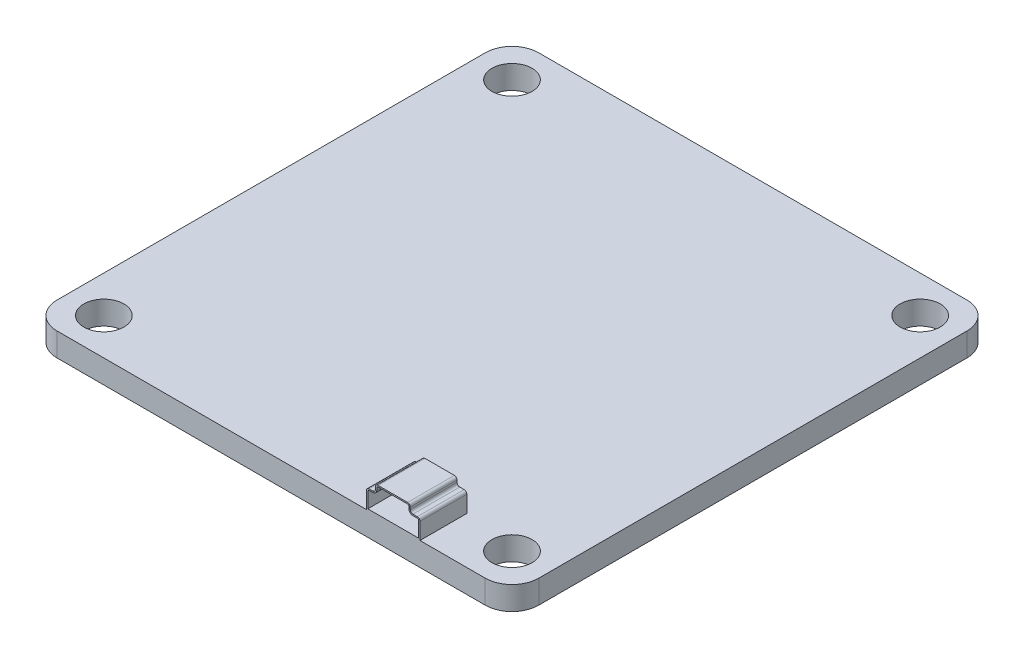
SolidWorks part; units mm, degrees
ref_plane "Front Plane" through (0, 0, 0) normal (0, 0, 1) x (1, 0, 0)
ref_plane "Top Plane" through (0, 0, 0) normal (0, 1, 0) x (1, 0, 0)
ref_plane "Right Plane" through (0, 0, 0) normal (1, 0, 0) x (0, 0, -1)
sketch "Sketch2" plane through (0, 0, 0) normal (0, 1, 0) x (1, 0, 0)
  line L1 (-16, 18) -> (16, 18)
  line L2 (-18, 16) -> (-18, -16)
  line L3 (-16, -18) -> (16, -18)
  line L4 (18, 16) -> (18, -16)
  line L5 (-18, 18) -> (18, -18) construction
  line L6 (-18, -18) -> (18, 18) construction
  line L7 (-15.25, 15.25) -> (15.25, 15.25) construction
  line L8 (-15.25, 15.25) -> (-15.25, -15.25) construction
  line L9 (-15.25, -15.25) -> (15.25, -15.25) construction
  line L10 (15.25, 15.25) -> (15.25, -15.25) construction
  line L11 (-15.25, 15.25) -> (15.25, -15.25) construction
  line L12 (-15.25, -15.25) -> (15.25, 15.25) construction
  circle A0 centre (-15.25, 15.25) radius 1.5
  circle A1 centre (15.25, 15.25) radius 1.5
  circle A2 centre (15.25, -15.25) radius 1.5
  circle A3 centre (-15.25, -15.25) radius 1.5
  arc A4 (16, -18) -> (18, -16) centre (16, -16) ccw
  arc A5 (-18, -16) -> (-16, -18) centre (-16, -16) ccw
  arc A6 (-16, 18) -> (-18, 16) centre (-16, 16) ccw
  arc A7 (16, 18) -> (18, 16) centre (16, 16) cw
  point P0 (0, 0)
  point P6 (0, 0)
  dimension "D5" = 3
  dimension "D6" = 2
  dimension "D1" = 36
  dimension "D2" = 36
  dimension "D3" = 30.5
  dimension "D4" = 30.5
extrude "Boss-Extrude1" add sketch "Sketch2" along normal blind 1.75
sketch "Sketch3" plane through (0, 0, 18) normal (0, 0, 1) x (1, 0, 0)
  line L0 (-16, 1.75) -> (16, 1.75) construction
  line L1 (7.1245, 1.75) -> (11.1245, 1.75)
  line L2 (7.1245, 1.75) -> (7.1245, 2.9923)
  line L3 (7.9938, 3.75) -> (10.1954, 3.75)
  line L4 (11.1245, 1.75) -> (11.1245, 2.9923)
  line L5 (7.7938, 3.55) -> (7.7938, 3.3923)
  line L6 (7.5938, 3.1923) -> (7.3245, 3.1923)
  line L7 (10.3954, 3.55) -> (10.3954, 3.3923)
  line L8 (10.5954, 3.1923) -> (10.9245, 3.1923)
  line L9 (7.9938, 3.65) -> (10.1954, 3.65)
  line L10 (10.2954, 3.55) -> (10.2954, 3.3923)
  line L11 (10.5954, 3.0923) -> (10.9245, 3.0923)
  line L12 (11.0245, 1.85) -> (11.0245, 2.9923)
  line L13 (7.2245, 1.85) -> (11.0245, 1.85)
  line L14 (7.2245, 1.85) -> (7.2245, 2.9923)
  line L15 (7.5938, 3.0923) -> (7.3245, 3.0923)
  line L16 (7.8938, 3.55) -> (7.8938, 3.3923)
  arc A0 (10.9245, 3.1923) -> (11.1245, 2.9923) centre (10.9245, 2.9923) cw
  arc A1 (10.3954, 3.3923) -> (10.5954, 3.1923) centre (10.5954, 3.3923) ccw
  arc A2 (10.3954, 3.55) -> (10.1954, 3.75) centre (10.1954, 3.55) ccw
  arc A3 (7.7938, 3.55) -> (7.9938, 3.75) centre (7.9938, 3.55) cw
  arc A4 (7.7938, 3.3923) -> (7.5938, 3.1923) centre (7.5938, 3.3923) cw
  arc A5 (7.3245, 3.1923) -> (7.1245, 2.9923) centre (7.3245, 2.9923) ccw
  arc A6 (10.2954, 3.55) -> (10.1954, 3.65) centre (10.1954, 3.55) ccw
  arc A7 (10.2954, 3.3923) -> (10.5954, 3.0923) centre (10.5954, 3.3923) ccw
  arc A8 (10.9245, 3.0923) -> (11.0245, 2.9923) centre (10.9245, 2.9923) cw
  arc A9 (7.3245, 3.0923) -> (7.2245, 2.9923) centre (7.3245, 2.9923) ccw
  arc A10 (7.8938, 3.3923) -> (7.5938, 3.0923) centre (7.5938, 3.3923) cw
  arc A11 (7.8938, 3.55) -> (7.9938, 3.65) centre (7.9938, 3.55) cw
  dimension "D1" = 0.2
  dimension "D2" = 0.1
extrude "Boss-Extrude2" add sketch "Sketch3" against normal blind 3
sketch "Sketch4" plane through (0, 0, 15) normal (0, 0, -1) x (-1, 0, 0)
  line L8 (-7.1245, 1.75) -> (-7.1245, 2.9923)
  line L9 (-7.3245, 3.1923) -> (-7.5938, 3.1923)
  line L10 (-7.7938, 3.3923) -> (-7.7938, 3.55)
  line L11 (-7.9938, 3.75) -> (-10.1954, 3.75)
  line L12 (-10.3954, 3.55) -> (-10.3954, 3.3923)
  line L13 (-10.5954, 3.1923) -> (-10.9245, 3.1923)
  line L14 (-11.1245, 2.9923) -> (-11.1245, 1.75)
  line L15 (-11.1245, 1.75) -> (-7.1245, 1.75)
  line L16 (-7.1245, 1.75) -> (-7.1245, 2.9923)
  line L17 (-7.3245, 3.1923) -> (-7.5938, 3.1923)
  line L18 (-7.7938, 3.3923) -> (-7.7938, 3.55)
  line L19 (-7.9938, 3.75) -> (-10.1954, 3.75)
  line L20 (-10.3954, 3.55) -> (-10.3954, 3.3923)
  line L21 (-10.5954, 3.1923) -> (-10.9245, 3.1923)
  line L22 (-11.1245, 2.9923) -> (-11.1245, 1.75)
  line L23 (-11.1245, 1.75) -> (-7.1245, 1.75)
  arc A6 (-7.1245, 2.9923) -> (-7.3245, 3.1923) centre (-7.3245, 2.9923) ccw
  arc A7 (-7.7938, 3.3923) -> (-7.5938, 3.1923) centre (-7.5938, 3.3923) ccw
  arc A8 (-7.7938, 3.55) -> (-7.9938, 3.75) centre (-7.9938, 3.55) ccw
  arc A9 (-10.1954, 3.75) -> (-10.3954, 3.55) centre (-10.1954, 3.55) ccw
  arc A10 (-10.5954, 3.1923) -> (-10.3954, 3.3923) centre (-10.5954, 3.3923) ccw
  arc A11 (-10.9245, 3.1923) -> (-11.1245, 2.9923) centre (-10.9245, 2.9923) ccw
  arc A12 (-7.1245, 2.9923) -> (-7.3245, 3.1923) centre (-7.3245, 2.9923) ccw
  arc A13 (-7.7938, 3.3923) -> (-7.5938, 3.1923) centre (-7.5938, 3.3923) ccw
  arc A14 (-7.7938, 3.55) -> (-7.9938, 3.75) centre (-7.9938, 3.55) ccw
  arc A15 (-10.1954, 3.75) -> (-10.3954, 3.55) centre (-10.1954, 3.55) ccw
  arc A16 (-10.5954, 3.1923) -> (-10.3954, 3.3923) centre (-10.5954, 3.3923) ccw
  arc A17 (-10.9245, 3.1923) -> (-11.1245, 2.9923) centre (-10.9245, 2.9923) ccw
  dimension "D1" = 0
extrude "Boss-Extrude3" add sketch "Sketch4" along normal blind 0.5
sketch "Sketch5" plane through (0, 0, 14.5) normal (0, 0, -1) x (-1, 0, 0)
  circle A0 centre (-10.1528, 2.6181) radius 0.25
  circle A1 centre (-9.3528, 2.6181) radius 0.25
  circle A2 centre (-8.5528, 2.6181) radius 0.25
  dimension "D1" = 0.5
  dimension "D2" = 0.8
  dimension "D3" = 0.8
extrude "Cut-Extrude1" cut sketch "Sketch5" against normal through all
